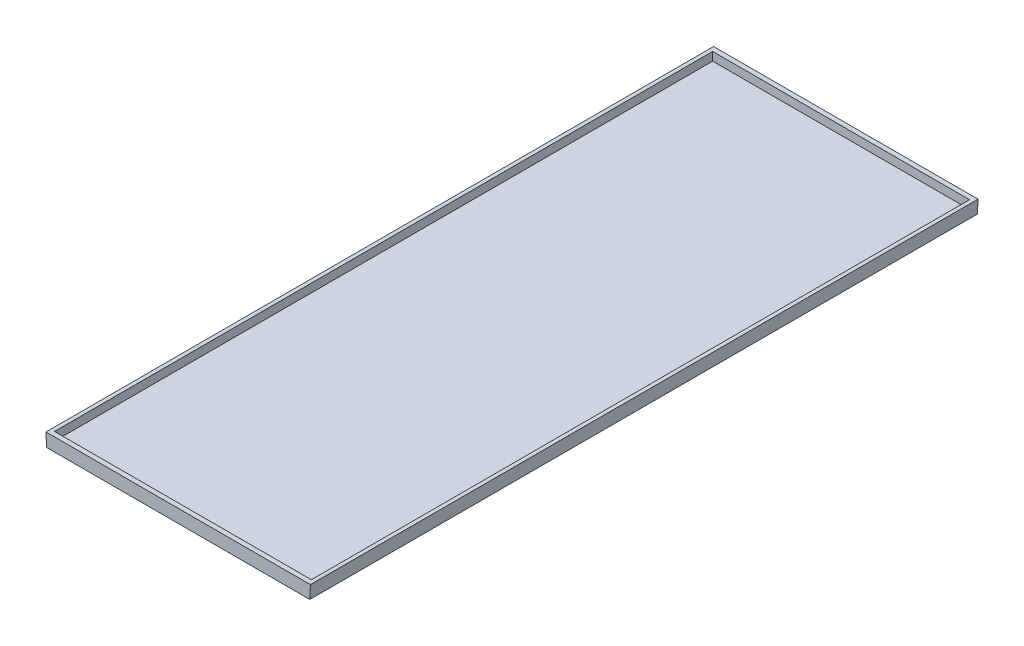
SolidWorks part; units mm, degrees
ref_plane "Front Plane" through (0, 0, 0) normal (0, 0, 1) x (1, 0, 0)
ref_plane "Top Plane" through (0, 0, 0) normal (0, 1, 0) x (1, 0, 0)
ref_plane "Right Plane" through (0, 0, 0) normal (1, 0, 0) x (0, 0, -1)
sketch "Sketch1" plane through (0, 0, 0) normal (0, 0, 1) x (1, 0, 0)
  line L1 (-70, -7) -> (70, -7)
  line L5 (70.3, 0) -> (-70.3, 0)
  line L10 (70, -7) -> (70.3, 0)
  line L11 (-70, -7) -> (-70.3, 0)
  dimension "D1" = 140.6
  dimension "D2" = 7
  dimension "D3" = 140
  dimension "D4" = 92.454
extrude "Boss-Extrude2" add sketch "Sketch1" along normal blind 355
sketch "Sketch2" plane through (0, 0, 0) normal (0, 1, 0) x (1, 0, 0)
  line L6 (0, 0) -> (0, -2.5)
  line L7 (-70.3, -177.5) -> (-68.3, -177.5)
  line L9 (-70.3, -355) -> (-70.3, 0) construction
  line L10 (70.3, -177.5) -> (68.3, -177.5)
  line L11 (70.3, -355) -> (70.3, 0) construction
  line L12 (0, -355) -> (0, -352.5)
  line L13 (70.3, -355) -> (-70.3, -355) construction
  line L15 (-68.3, -352.5) -> (68.3, -352.5)
  line L16 (-68.3, -352.5) -> (-68.3, -2.5)
  line L17 (-68.3, -2.5) -> (68.3, -2.5)
  line L18 (68.3, -352.5) -> (68.3, -2.5)
  dimension "D1" = 2
  dimension "D2" = 2
  dimension "D3" = 2.5
extrude "Cut-Extrude1" cut sketch "Sketch2" against normal blind 4.5 contours L15 L18 L17 L16
